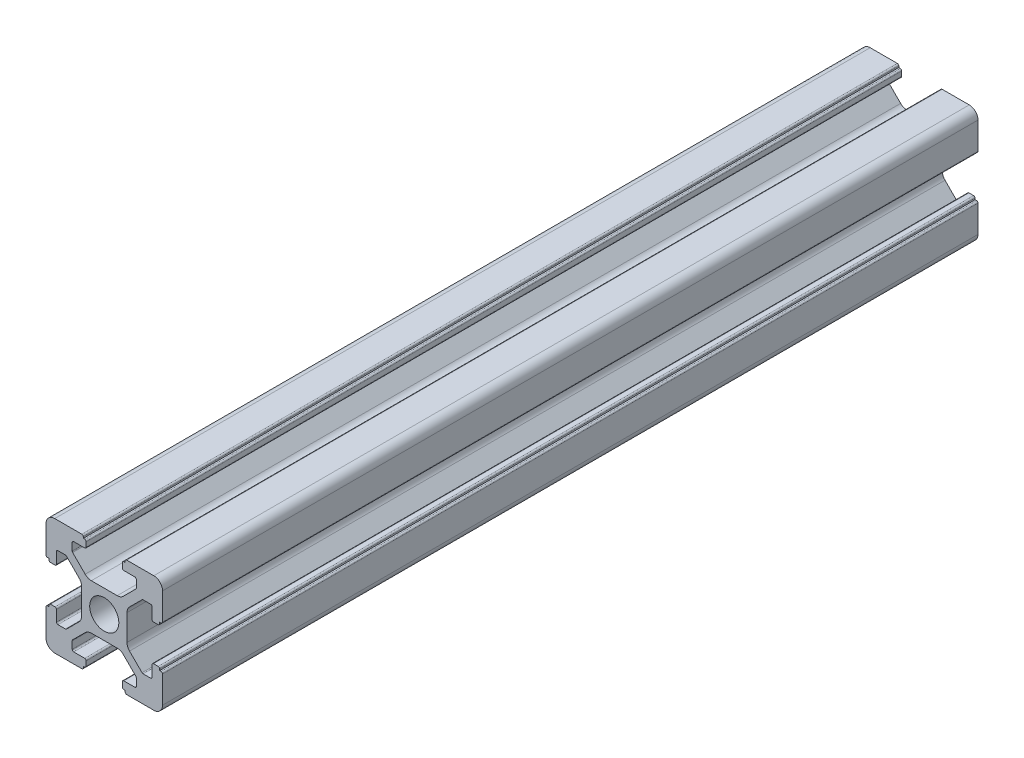
SolidWorks part; units mm, degrees
ref_plane "前视基准面" through (0, 0, 0) normal (0, 0, 1) x (1, 0, 0)
ref_plane "上视基准面" through (0, 0, 0) normal (0, 1, 0) x (1, 0, 0)
ref_plane "右视基准面" through (0, 0, 0) normal (1, 0, 0) x (0, 0, -1)
sketch "草图1" plane through (0, 0, 0) normal (0, 0, 1) x (1, 0, 0)
  line L0 (0, 0) -> (0, 5.5) construction
  line L1 (-8.5023, -10.0023) -> (-3.85, -10.0023)
  line L2 (-10.0023, -8.5023) -> (-10.0023, -3.85)
  line L3 (-8.5023, 10.0023) -> (-3.85, 10.0023)
  line L4 (10.0023, -8.5023) -> (10.0023, -3.85)
  line L5 (-10.0023, -10.0023) -> (10.0023, 10.0023) construction
  line L6 (-10.0023, 10.0023) -> (10.0023, -10.0023) construction
  line L7 (-2.218, -3.9) -> (2.218, -3.9)
  line L8 (-3.9, -2.218) -> (-3.9, 2.218)
  line L9 (-2.218, 3.9) -> (2.218, 3.9)
  line L10 (3.9, -2.218) -> (3.9, 2.218)
  line L11 (-3.9, -3.9) -> (3.9, 3.9) construction
  line L12 (-3.9, 3.9) -> (3.9, -3.9) construction
  line L13 (-5.25, -8.2) -> (-3.35, -8.2)
  line L14 (-8.2, -5.25) -> (-8.2, -3.35)
  line L15 (-5.25, 8.2) -> (-3.35, 8.2)
  line L16 (8.2, -5.25) -> (8.2, -3.35)
  line L17 (-8.2, -8.2) -> (8.2, 8.2) construction
  line L18 (-8.2, 8.2) -> (8.2, -8.2) construction
  line L19 (-7.95, 5.5) -> (-6.6642, 5.5)
  line L20 (0, 0) -> (5.5, 0) construction
  line L23 (-5.5, 7.95) -> (-5.5, 6.6642)
  line L26 (0, 0) -> (-0.5303, 0.5303)
  line L27 (3.2787, 4.3393) -> (5.4268, 6.4874)
  line L28 (0, 0) -> (0.5303, -0.5303)
  line L29 (5.5, 6.6642) -> (5.5, 7.95)
  line L30 (4.3393, 3.2787) -> (6.4874, 5.4268)
  line L31 (6.6642, 5.5) -> (7.95, 5.5)
  line L32 (4.3393, -3.2787) -> (6.4874, -5.4268)
  line L33 (3.2787, -4.3393) -> (5.4268, -6.4874)
  line L34 (-3.2787, -4.3393) -> (-5.4268, -6.4874)
  line L35 (-4.3393, -3.2787) -> (-6.4874, -5.4268)
  line L36 (-4.3393, 3.2787) -> (-6.4874, 5.4268)
  line L37 (-3.2787, 4.3393) -> (-5.4268, 6.4874)
  line L38 (3.1, -8.45) -> (3.1, -9.2523)
  line L39 (8.45, 3.1) -> (9.2523, 3.1)
  line L40 (-5.5, -6.6642) -> (-5.5, -7.95)
  line L41 (-6.6642, -5.5) -> (-7.95, -5.5)
  line L42 (5.5, -6.6642) -> (5.5, -7.95)
  line L43 (6.6642, -5.5) -> (7.95, -5.5)
  line L44 (9.2523, -3.1) -> (8.45, -3.1)
  line L46 (10.0023, 3.85) -> (10.0023, 8.5023)
  line L47 (8.2, 3.35) -> (8.2, 5.25)
  line L48 (-3.1, -9.2523) -> (-3.1, -8.45)
  line L49 (-8.45, -3.1) -> (-9.2523, -3.1)
  line L50 (-9.2523, 3.1) -> (-8.45, 3.1)
  line L51 (-3.1, 8.45) -> (-3.1, 9.2523)
  line L52 (3.1, 9.2523) -> (3.1, 8.45)
  line L53 (3.85, 10.0023) -> (8.5023, 10.0023)
  line L54 (3.35, 8.2) -> (5.25, 8.2)
  line L55 (-10.0023, 3.85) -> (-10.0023, 8.5023)
  line L56 (-8.2, 3.35) -> (-8.2, 5.25)
  line L57 (3.35, -8.2) -> (5.25, -8.2)
  line L58 (3.85, -10.0023) -> (8.5023, -10.0023)
  line L59 (9.7523, -3.6) -> (9.5023, -3.6)
  line L61 (9.7523, 3.6) -> (9.5023, 3.6)
  line L62 (9.5023, -3.6) -> (9.5023, -3.35)
  line L63 (3.6, -9.7523) -> (3.6, -9.5023)
  line L64 (3.35, -9.5023) -> (3.6, -9.5023)
  line L65 (9.5023, 3.35) -> (9.5023, 3.6)
  line L66 (-3.6, -9.5023) -> (-3.35, -9.5023)
  line L67 (-3.6, -9.7523) -> (-3.6, -9.5023)
  line L68 (-9.7523, -3.6) -> (-9.5023, -3.6)
  line L69 (-9.5023, -3.35) -> (-9.5023, -3.6)
  line L70 (-9.5023, 3.6) -> (-9.5023, 3.35)
  line L71 (-9.7523, 3.6) -> (-9.5023, 3.6)
  line L72 (-3.6, 9.7523) -> (-3.6, 9.5023)
  line L73 (-3.35, 9.5023) -> (-3.6, 9.5023)
  line L74 (3.6, 9.5023) -> (3.35, 9.5023)
  line L75 (3.6, 9.7523) -> (3.6, 9.5023)
  circle A0 centre (0, 0) radius 2.5
  arc A1 (10.0023, 8.5023) -> (8.5023, 10.0023) centre (8.5023, 8.5023) ccw
  arc A2 (8.5023, -10.0023) -> (10.0023, -8.5023) centre (8.5023, -8.5023) ccw
  arc A3 (-10.0023, -8.5023) -> (-8.5023, -10.0023) centre (-8.5023, -8.5023) ccw
  arc A4 (-10.0023, 8.5023) -> (-8.5023, 10.0023) centre (-8.5023, 8.5023) cw
  arc A5 (-9.5023, -3.35) -> (-9.2523, -3.1) centre (-9.2523, -3.35) cw
  arc A6 (-9.7523, -3.6) -> (-10.0023, -3.85) centre (-9.7523, -3.85) ccw
  arc A7 (-8.45, -3.1) -> (-8.2, -3.35) centre (-8.45, -3.35) cw
  arc A8 (-7.95, -5.5) -> (-8.2, -5.25) centre (-7.95, -5.25) cw
  arc A9 (-6.4874, -5.4268) -> (-6.6642, -5.5) centre (-6.6642, -5.25) cw
  arc A10 (-5.4268, -6.4874) -> (-5.5, -6.6642) centre (-5.25, -6.6642) ccw
  arc A11 (-5.5, -7.95) -> (-5.25, -8.2) centre (-5.25, -7.95) ccw
  arc A12 (-3.6, -9.7523) -> (-3.85, -10.0023) centre (-3.85, -9.7523) cw
  arc A13 (-3.35, -9.5023) -> (-3.1, -9.2523) centre (-3.35, -9.2523) ccw
  arc A14 (-3.1, -8.45) -> (-3.35, -8.2) centre (-3.35, -8.45) ccw
  arc A15 (3.1, -8.45) -> (3.35, -8.2) centre (3.35, -8.45) cw
  arc A16 (5.5, -7.95) -> (5.25, -8.2) centre (5.25, -7.95) cw
  arc A17 (5.4268, -6.4874) -> (5.5, -6.6642) centre (5.25, -6.6642) cw
  arc A18 (6.4874, -5.4268) -> (6.6642, -5.5) centre (6.6642, -5.25) ccw
  arc A19 (7.95, -5.5) -> (8.2, -5.25) centre (7.95, -5.25) ccw
  arc A20 (8.45, -3.1) -> (8.2, -3.35) centre (8.45, -3.35) ccw
  arc A21 (9.5023, -3.35) -> (9.2523, -3.1) centre (9.2523, -3.35) ccw
  arc A22 (9.7523, -3.6) -> (10.0023, -3.85) centre (9.7523, -3.85) cw
  arc A23 (3.35, -9.5023) -> (3.1, -9.2523) centre (3.35, -9.2523) cw
  arc A24 (3.6, -9.7523) -> (3.85, -10.0023) centre (3.85, -9.7523) ccw
  arc A25 (7.95, 5.5) -> (8.2, 5.25) centre (7.95, 5.25) cw
  arc A26 (8.2, 3.35) -> (8.45, 3.1) centre (8.45, 3.35) ccw
  arc A27 (9.5023, 3.35) -> (9.2523, 3.1) centre (9.2523, 3.35) cw
  arc A28 (9.7523, 3.6) -> (10.0023, 3.85) centre (9.7523, 3.85) ccw
  arc A29 (6.6642, 5.5) -> (6.4874, 5.4268) centre (6.6642, 5.25) ccw
  arc A30 (5.4268, 6.4874) -> (5.5, 6.6642) centre (5.25, 6.6642) ccw
  arc A31 (5.5, 7.95) -> (5.25, 8.2) centre (5.25, 7.95) ccw
  arc A32 (3.1, 8.45) -> (3.35, 8.2) centre (3.35, 8.45) ccw
  arc A33 (3.6, 9.7523) -> (3.85, 10.0023) centre (3.85, 9.7523) cw
  arc A34 (3.35, 9.5023) -> (3.1, 9.2523) centre (3.35, 9.2523) ccw
  arc A35 (-9.7523, 3.6) -> (-10.0023, 3.85) centre (-9.7523, 3.85) cw
  arc A36 (-9.5023, 3.35) -> (-9.2523, 3.1) centre (-9.2523, 3.35) ccw
  arc A37 (-8.45, 3.1) -> (-8.2, 3.35) centre (-8.45, 3.35) ccw
  arc A38 (-8.2, 5.25) -> (-7.95, 5.5) centre (-7.95, 5.25) cw
  arc A39 (-6.4874, 5.4268) -> (-6.6642, 5.5) centre (-6.6642, 5.25) ccw
  arc A40 (-5.4268, 6.4874) -> (-5.5, 6.6642) centre (-5.25, 6.6642) cw
  arc A41 (-5.5, 7.95) -> (-5.25, 8.2) centre (-5.25, 7.95) cw
  arc A42 (-3.1, 8.45) -> (-3.35, 8.2) centre (-3.35, 8.45) cw
  arc A43 (-3.1, 9.2523) -> (-3.35, 9.5023) centre (-3.35, 9.2523) ccw
  arc A44 (-3.6, 9.7523) -> (-3.85, 10.0023) centre (-3.85, 9.7523) ccw
  arc A45 (-4.3393, 3.2787) -> (-3.9, 2.218) centre (-5.4, 2.218) cw
  arc A46 (-3.2787, 4.3393) -> (-2.218, 3.9) centre (-2.218, 5.4) ccw
  arc A47 (3.2787, 4.3393) -> (2.218, 3.9) centre (2.218, 5.4) cw
  arc A48 (4.3393, 3.2787) -> (3.9, 2.218) centre (5.4, 2.218) ccw
  arc A49 (4.3393, -3.2787) -> (3.9, -2.218) centre (5.4, -2.218) cw
  arc A50 (3.2787, -4.3393) -> (2.218, -3.9) centre (2.218, -5.4) ccw
  arc A51 (-4.3393, -3.2787) -> (-3.9, -2.218) centre (-5.4, -2.218) ccw
  arc A52 (-2.218, -3.9) -> (-3.2787, -4.3393) centre (-2.218, -5.4) ccw
  point P0 (0, 0)
  point P7 (10.0023, 0)
  point P62 (0, 0)
  point P76 (0, 0)
  point P92 (-8.2, -5.5)
  point P99 (0, 0)
  point P106 (-5.5, -8.2)
  point P117 (5.5, -8.2)
  point P124 (8.2, -5.5)
  point P137 (8.2, 5.5)
  point P140 (8.2, 3.1)
  point P147 (6.5607, 5.5)
  point P152 (5.5, 8.2)
  point P167 (-8.2, 5.5)
  point P174 (-5.5, 8.2)
  dimension "D1" = 1.5
  dimension "D5" = 0.25
  dimension "D6" = 1.5
  dimension "D2" = 4
  dimension "D3" = 4
  dimension "D4" = 4
extrude "凸台-拉伸1" add sketch "草图1" along normal blind 140 contours A52 L7 A50 L33 A17 L42 A16 L57 A15 L38 A23 L64 L63 A24 L58 A2 L4 A22 L59 L62 A21 L44 A20 L16 A19 L43 A18 L32 A49 L10 A48 L30 A29 L31 A25 L47 A26 L39 A27 L65 L61 A28 L46 A1 L53 A33 L75 L74 A34 L52 A32
ref_plane "Plane1" through (0, 0, 70) normal (0, 0, 1) x (1, 0, 0)
